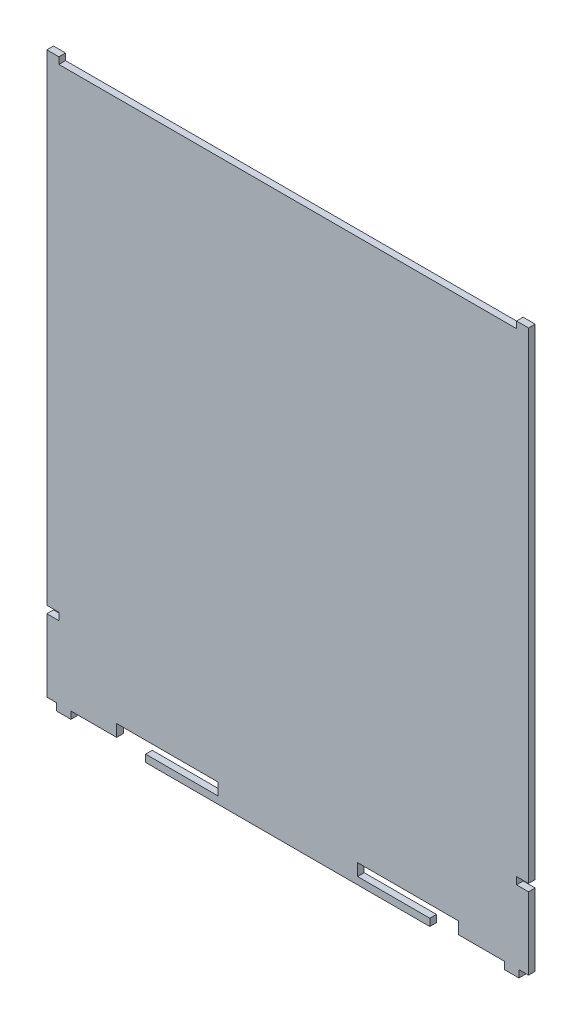
SolidWorks part; units mm, degrees
ref_plane "前视基准面" through (0, 0, 0) normal (0, 0, 1) x (1, 0, 0)
ref_plane "上视基准面" through (0, 0, 0) normal (0, 1, 0) x (1, 0, 0)
ref_plane "右视基准面" through (0, 0, 0) normal (1, 0, 0) x (0, 0, -1)
sketch "草图1" plane through (0, 0, 0) normal (0, 0, 1) x (1, 0, 0)
  line L0 (0, 0) -> (4, 0)
  line L1 (0, 0) -> (4, 0)
  line L2 (0, 0) -> (0, 27)
  line L4 (200, 0) -> (200, 27)
  line L6 (0, 33) -> (0, 230)
  line L7 (5, 230) -> (195, 230)
  line L8 (200, 33) -> (200, 230)
  line L9 (4, 0) -> (4, -3)
  line L10 (4, -3) -> (10, -3)
  line L11 (10, -3) -> (10, 0)
  line L12 (200, 0) -> (196, 0)
  line L13 (196, 0) -> (196, -3)
  line L14 (196, -3) -> (190, -3)
  line L15 (190, -3) -> (190, 0)
  line L16 (0, 0) -> (4, 0)
  line L17 (29, 0) -> (29, 5)
  line L18 (200, 0) -> (196, 0)
  line L19 (29, 5) -> (71, 5)
  line L20 (159, -3) -> (41, -3)
  line L21 (171, 0) -> (190, 0)
  line L22 (0, 0) -> (4, 0)
  line L23 (41, 0) -> (41, -3)
  line L24 (200, 0) -> (196, 0)
  line L25 (159, 0) -> (159, -3)
  line L26 (71, 5) -> (71, 0)
  line L27 (71, 0) -> (41, 0)
  line L28 (171, 0) -> (171, 5)
  line L29 (171, 5) -> (129, 5)
  line L30 (129, 5) -> (129, 0)
  line L31 (129, 0) -> (159, 0)
  line L32 (0, 27) -> (0, 30)
  line L33 (195, 30) -> (195, 33)
  line L34 (195, 33) -> (200, 33)
  line L35 (200, 30) -> (195, 30)
  line L38 (195, 30) -> (200, 30)
  line L39 (200, 33) -> (200, 230)
  line L40 (190, 0) -> (171, 0)
  line L41 (196, 0) -> (200, 0)
  line L42 (190, 0) -> (159, 0)
  line L43 (10, 0) -> (29, 0)
  line L44 (10, 0) -> (29, 0)
  line L45 (10, 0) -> (41, 0)
  line L46 (0, 230) -> (0, 232.75)
  line L47 (0, 232.75) -> (5, 232.75)
  line L48 (5, 232.75) -> (5, 230)
  line L49 (200, 230) -> (200, 232.75)
  line L50 (200, 232.75) -> (195, 232.75)
  line L51 (195, 232.75) -> (195, 230)
  line L52 (5, 30) -> (5, 33)
  line L53 (5, 33) -> (0, 33)
  line L54 (0, 30) -> (5, 30)
  line L55 (200, 27) -> (200, 30)
extrude "凸台-拉伸2" add sketch "草图1" along normal blind 2.75 contours L4 L55 L35 L33 L34 L8 L49 L50 L51 L7 L48 L47 L46 L6 L53 L52 L54 L32 L2 L0 L9 L10 L11 L43 L17 L19 L26 L27 L23 L20 L25 L31 L30 L29 L28 L21 L15 L14 L13 L12
